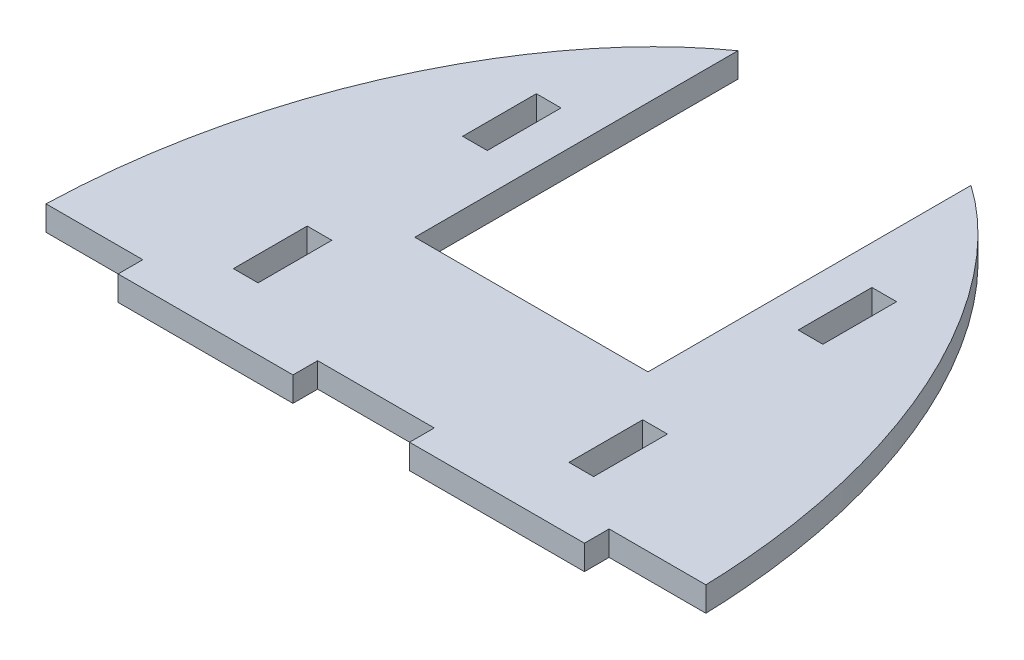
SolidWorks part; units mm, degrees
ref_plane "Front Plane" through (0, 0, 0) normal (0, 0, 1) x (1, 0, 0)
ref_plane "Top Plane" through (0, 0, 0) normal (0, 1, 0) x (1, 0, 0)
ref_plane "Right Plane" through (0, 0, 0) normal (1, 0, 0) x (0, 0, -1)
sketch "Sketch1" plane through (0, 0, 0) normal (0, 1, 0) x (1, 0, 0)
  line L0 (0, 0) -> (85, 0)
  line L1 (42.5, 0) -> (42.5, 70)
  line L2 (70.0314, 70) -> (13.9721, 70) construction
  line L3 (0, 35.1141) -> (0, -35.1141) construction
  line L4 (85, -45.8948) -> (85, 45.8948) construction
  spline S0 degree 3 poles (0, 0) (0, 36) (22.55, 70.2833) (62.45, 70.2833) (85, 36) (85, 0) knots 0 0 0 0 0.45 0.55 1 1 1 1
  dimension "D3" = 120
  dimension "D4" = 120
  dimension "D5" = 120
  dimension "D1" = 85
  dimension "D2" = 70
extrude "Boss-Extrude1" add sketch "Sketch1" along normal blind 3.175 contours S0 L0 L1 | S0 L1 L0
sketch "Sketch2" plane through (0, 3.175, 0) normal (0, 1, 0) x (1, 0, 0)
  line L0 (0, 0) -> (85, 0) construction
  line L1 (19.325, 46.992) -> (22.5, 46.992)
  line L2 (19.325, 46.992) -> (19.325, 37.5)
  line L3 (19.325, 37.5) -> (22.5, 37.5)
  line L4 (22.5, 46.992) -> (22.5, 37.5)
  line L5 (62.5, 46.992) -> (65.675, 46.992)
  line L6 (62.5, 46.992) -> (62.5, 37.5)
  line L7 (62.5, 37.5) -> (65.675, 37.5)
  line L8 (65.675, 46.992) -> (65.675, 37.5)
  line L9 (19.325, 17.5) -> (22.5, 17.5)
  line L10 (19.325, 17.5) -> (19.325, 8.008)
  line L11 (19.325, 8.008) -> (22.5, 8.008)
  line L12 (22.5, 17.5) -> (22.5, 8.008)
  line L13 (62.5, 17.5) -> (65.675, 17.5)
  line L14 (62.5, 17.5) -> (62.5, 8.008)
  line L15 (62.5, 8.008) -> (65.675, 8.008)
  line L16 (65.675, 17.5) -> (65.675, 8.008)
  line L18 (0, 0) -> (12.5, 0)
  line L19 (0, 0) -> (0, 3.175)
  line L20 (0, 3.175) -> (12.5, 3.175)
  line L21 (12.5, 0) -> (12.5, 3.175)
  line L22 (35, 0) -> (50, 0)
  line L23 (35, 0) -> (35, 3.175)
  line L24 (35, 3.175) -> (50, 3.175)
  line L25 (50, 0) -> (50, 3.175)
  line L26 (85, 0) -> (72.5, 0)
  line L27 (85, 0) -> (85, 3.175)
  line L28 (85, 3.175) -> (72.5, 3.175)
  line L29 (72.5, 0) -> (72.5, 3.175)
  line L30 (27.5, 78.2349) -> (57.5, 78.2349)
  line L31 (27.5, 78.2349) -> (27.5, 23.175)
  line L32 (27.5, 23.175) -> (57.5, 23.175)
  line L33 (57.5, 78.2349) -> (57.5, 23.175)
  spline S0 degree 3 poles (0, 0) (0, 36) (22.55, 70.2833) (62.45, 70.2833) (85, 36) (85, 0) knots 0 0 0 0 0.45 0.55 1 1 1 1 construction
  point P38 (42.5, 23.175)
  point P39 (42.5, 3.175)
  dimension "D1" = 9.492
  dimension "D2" = 9.492
  dimension "D3" = 20
  dimension "D4" = 8.008
  dimension "D5" = 12.5
  dimension "D6" = 12.5
  dimension "D7" = 15
  dimension "D8" = 22.5
  dimension "D9" = 3.175
  dimension "D10" = 20
  dimension "D11" = 30
extrude "Cut-Extrude1" cut sketch "Sketch2" against normal through all
